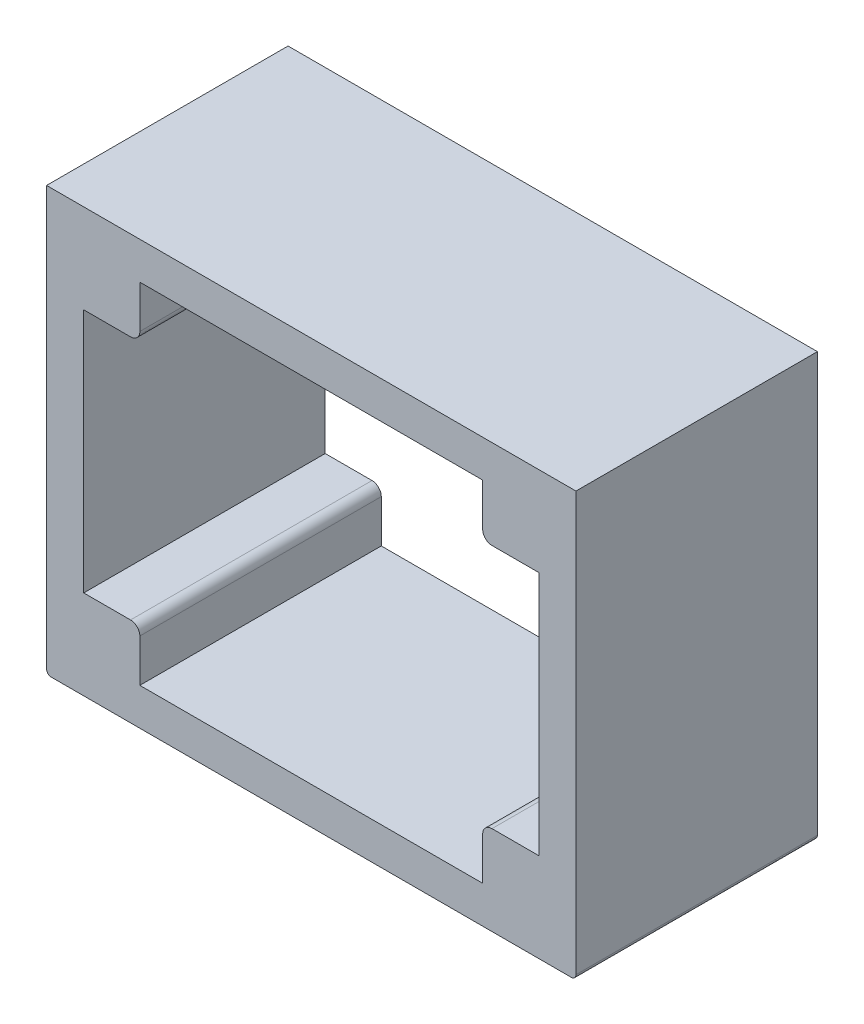
SolidWorks part; units mm, degrees
ref_plane "Front Plane" through (0, 0, 0) normal (0, 0, 1) x (1, 0, 0)
ref_plane "Top Plane" through (0, 0, 0) normal (0, 1, 0) x (1, 0, 0)
ref_plane "Right Plane" through (0, 0, 0) normal (1, 0, 0) x (0, 0, -1)
sketch "Sketch1" plane through (0, 0, 0) normal (0, 0, 1) x (1, 0, 0)
  line L4 (174.498, 0) -> (-6.477, 0)
  line L5 (-6.477, 0) -> (-6.477, -143.1925)
  line L6 (-4.8895, -144.78) -> (172.9105, -144.78)
  line L7 (174.498, -143.1925) -> (174.498, 0)
  line L8 (174.498, 0) -> (-6.477, 0)
  line L9 (-6.477, 0) -> (-6.477, -143.1925)
  line L10 (-4.8895, -144.78) -> (172.9105, -144.78)
  line L11 (174.498, -143.1925) -> (174.498, 0)
  line L16 (6.223, -114.3) -> (22.225, -114.3)
  line L17 (142.621, -12.7) -> (25.4, -12.7)
  line L18 (6.223, -114.3) -> (22.225, -114.3)
  line L19 (161.798, -114.3) -> (161.798, -30.48)
  line L20 (22.225, -30.48) -> (6.223, -30.48)
  line L21 (25.4, -132.08) -> (142.621, -132.08)
  line L22 (22.225, -30.48) -> (6.223, -30.48)
  line L23 (6.223, -30.48) -> (6.223, -114.3)
  line L24 (25.4, -12.7) -> (25.4, -27.305)
  line L25 (142.621, -12.7) -> (25.4, -12.7)
  line L26 (25.4, -12.7) -> (25.4, -27.305)
  line L27 (161.798, -114.3) -> (161.798, -30.48)
  line L28 (142.621, -27.305) -> (142.621, -12.7)
  line L29 (25.4, -132.08) -> (142.621, -132.08)
  line L30 (142.621, -27.305) -> (142.621, -12.7)
  line L31 (6.223, -30.48) -> (6.223, -114.3)
  line L404 (161.798, -30.48) -> (145.796, -30.48)
  line L405 (161.798, -30.48) -> (145.796, -30.48)
  line L406 (145.796, -114.3) -> (161.798, -114.3)
  line L407 (145.796, -114.3) -> (161.798, -114.3)
  line L408 (142.621, -132.08) -> (142.621, -117.475)
  line L409 (142.621, -132.08) -> (142.621, -117.475)
  line L410 (25.4, -117.475) -> (25.4, -132.08)
  line L411 (25.4, -117.475) -> (25.4, -132.08)
  arc A4 (172.9105, -144.78) -> (174.498, -143.1925) centre (172.9105, -143.1925) ccw
  arc A5 (172.9105, -144.78) -> (174.498, -143.1925) centre (172.9105, -143.1925) ccw
  arc A6 (-6.477, -143.1925) -> (-4.8895, -144.78) centre (-4.8895, -143.1925) ccw
  arc A7 (-6.477, -143.1925) -> (-4.8895, -144.78) centre (-4.8895, -143.1925) ccw
  arc A16 (22.225, -30.48) -> (25.4, -27.305) centre (22.225, -27.305) ccw
  arc A17 (22.225, -30.48) -> (25.4, -27.305) centre (22.225, -27.305) ccw
  arc A18 (142.621, -27.305) -> (145.796, -30.48) centre (145.796, -27.305) ccw
  arc A19 (142.621, -27.305) -> (145.796, -30.48) centre (145.796, -27.305) ccw
  arc A20 (145.796, -114.3) -> (142.621, -117.475) centre (145.796, -117.475) ccw
  arc A21 (145.796, -114.3) -> (142.621, -117.475) centre (145.796, -117.475) ccw
  arc A22 (25.4, -117.475) -> (22.225, -114.3) centre (22.225, -117.475) ccw
  arc A23 (25.4, -117.475) -> (22.225, -114.3) centre (22.225, -117.475) ccw
  dimension "D1" = 0
  dimension "D2" = 0
extrude "Boss-Extrude1" add sketch "Sketch1" along normal blind 82.55
